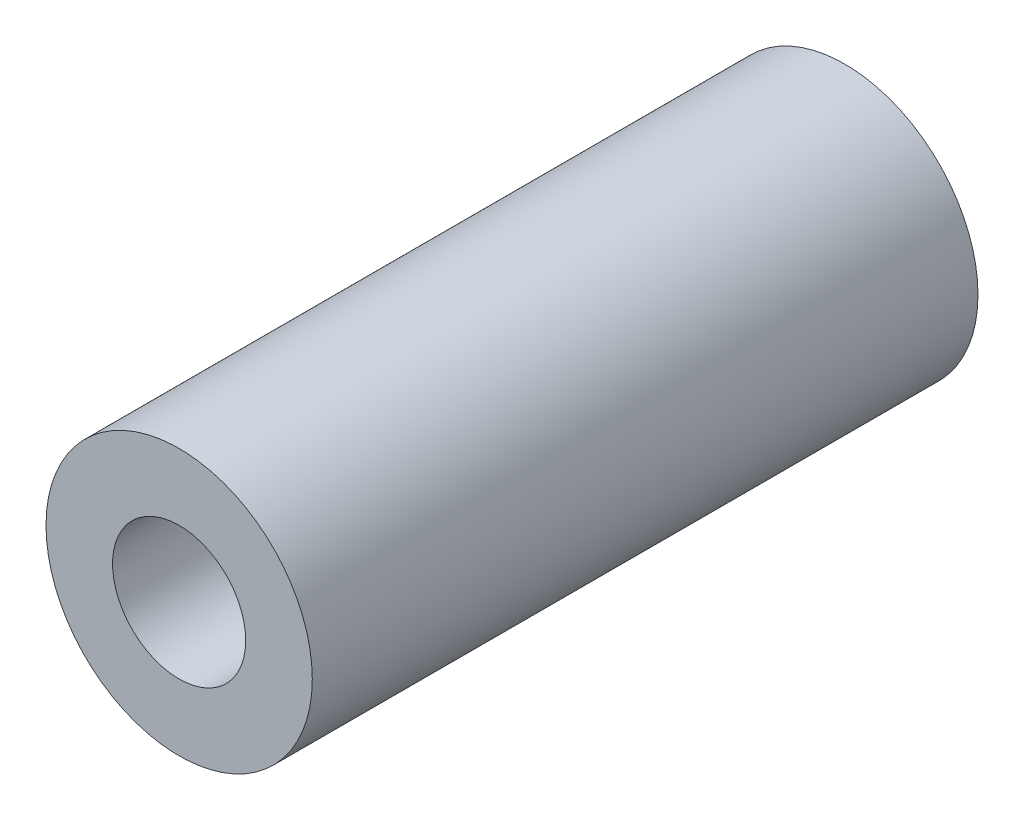
SolidWorks part; units mm, degrees
ref_plane "前视基准面" through (0, 0, 0) normal (0, 0, 1) x (1, 0, 0)
ref_plane "上视基准面" through (0, 0, 0) normal (0, 1, 0) x (1, 0, 0)
ref_plane "右视基准面" through (0, 0, 0) normal (1, 0, 0) x (0, 0, -1)
sketch "草图1" plane through (0, 0, 0) normal (0, 0, 1) x (1, 0, 0)
  circle A0 centre (0, 0) radius 3
  circle A1 centre (0, 0) radius 1.5
  dimension "D1" = 3
  dimension "D2" = 6
extrude "凸台-拉伸1" add sketch "草图1" along normal mid plane 15
